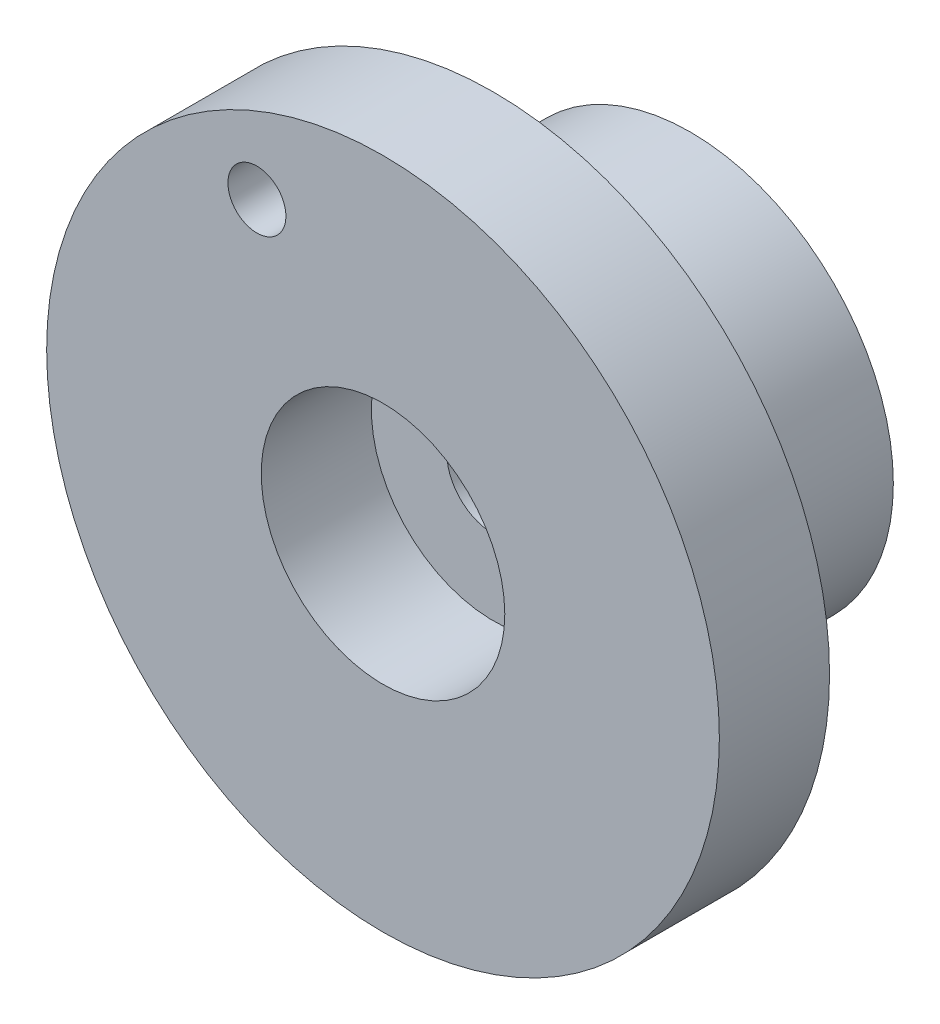
SolidWorks part; units mm, degrees
ref_plane "Front" through (0, 0, 0) normal (0, 0, 1) x (1, 0, 0)
ref_plane "Top" through (0, 0, 0) normal (0, 1, 0) x (1, 0, 0)
ref_plane "Right" through (0, 0, 0) normal (1, 0, 0) x (0, 0, -1)
other "Configuration Table"
sketch "Эскиз1" plane through (0, 0, 0) normal (0, 0, 1) x (1, 0, 0)
  circle A0 centre (0, 0) radius 29
  circle A1 centre (0, 0) radius 10.5
extrude "Бобышка-Вытянуть1" add sketch "Эскиз1" along normal blind 9.5
sketch "Эскиз2" plane through (0, 0, 0) normal (0, 0, -1) x (-1, 0, 0)
  circle A0 centre (0, 0) radius 17.5
  circle A1 centre (0, 0) radius 4
extrude "Бобышка-Вытянуть2" add sketch "Эскиз2" along normal blind 17
sketch "Эскиз3" plane through (0, 0, 9.5) normal (0, 0, 1) x (1, 0, 0)
  circle A0 centre (-10.8717, 20.2683) radius 2.5
  circle A2 centre (0, 0) radius 29 construction
  dimension "D1" = 23
extrude "Вырез-Вытянуть1" cut sketch "Эскиз3" against normal blind 17
